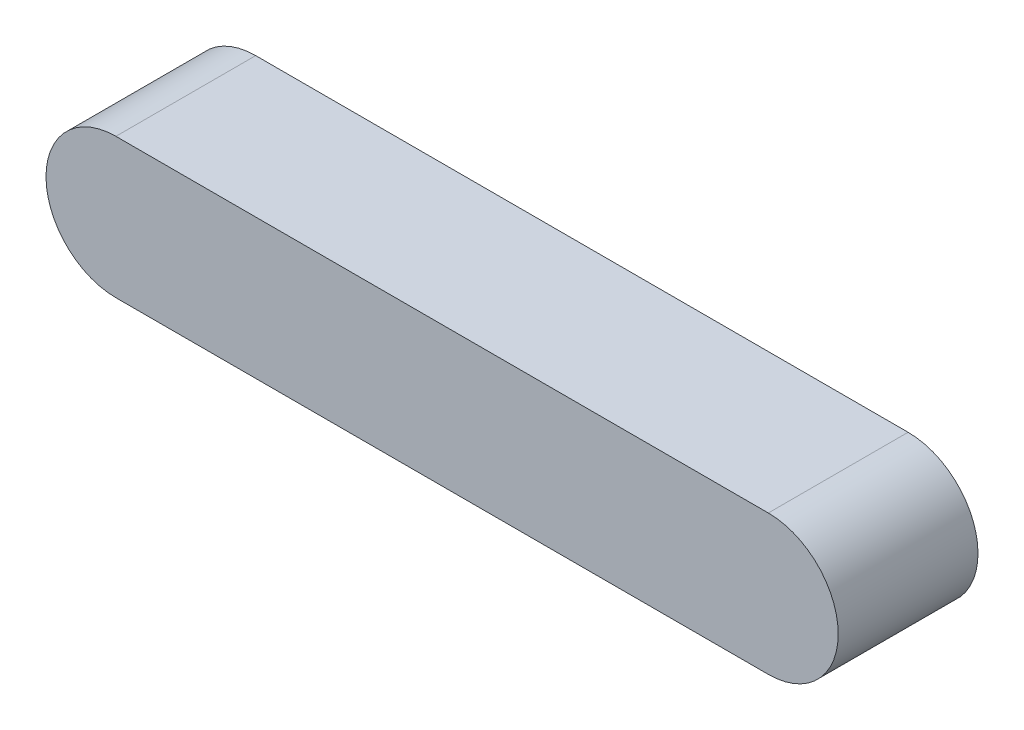
SolidWorks part; units mm, degrees
material "AISI 1020 钢，冷轧"
ref_plane "前视基准面" through (0, 0, 0) normal (0, 0, 1) x (1, 0, 0)
ref_plane "上视基准面" through (0, 0, 0) normal (0, 1, 0) x (1, 0, 0)
ref_plane "右视基准面" through (0, 0, 0) normal (1, 0, 0) x (0, 0, -1)
sketch "草图1" plane through (0, 0, 0) normal (0, 0, 1) x (1, 0, 0)
  line L0 (0, 0) -> (70, 0)
  line L1 (70, 0) -> (70, 15) construction
  line L2 (70, 15) -> (0, 15)
  line L3 (0, 15) -> (0, 0) construction
  arc A0 (0, 15) -> (0, 0) centre (0, 7.5) ccw
  arc A1 (70, 0) -> (70, 15) centre (70, 7.5) ccw
  dimension "D1" = 70
  dimension "D2" = 15
extrude "凸台-拉伸1" add sketch "草图1" along normal blind 15
